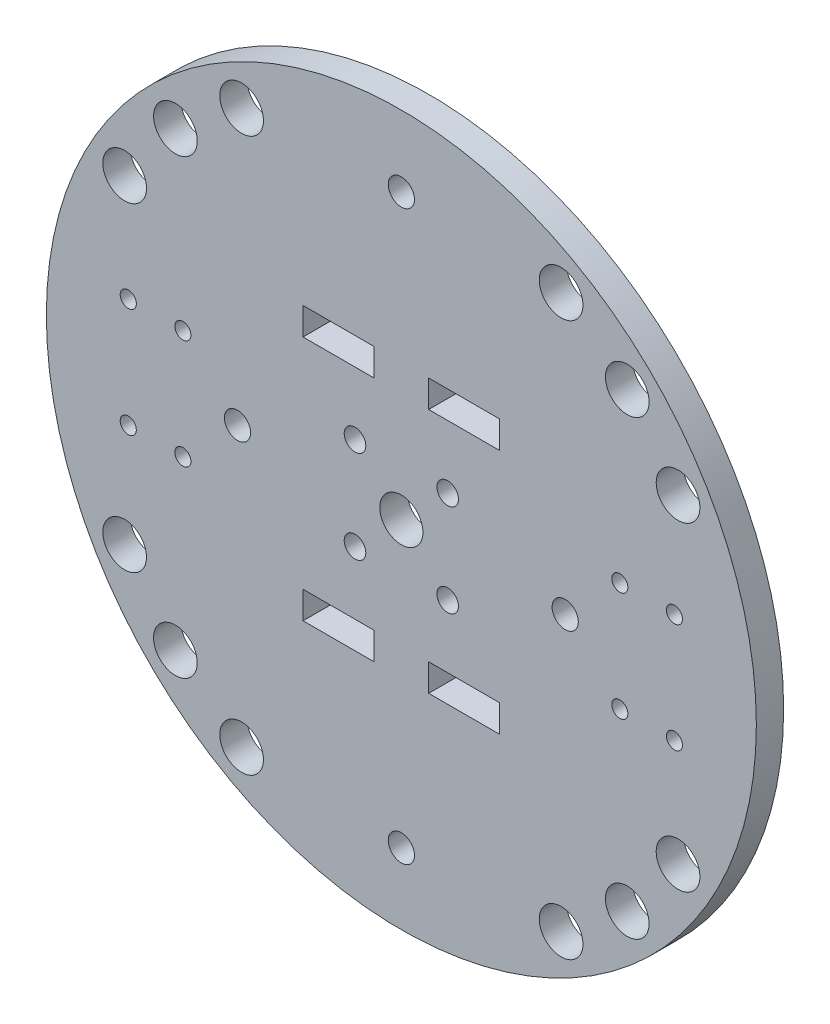
SolidWorks part; units mm, degrees
ref_plane "Front Plane" through (0, 0, 0) normal (0, 0, 1) x (1, 0, 0)
ref_plane "Top Plane" through (0, 0, 0) normal (0, 1, 0) x (1, 0, 0)
ref_plane "Right Plane" through (0, 0, 0) normal (1, 0, 0) x (0, 0, -1)
sketch "Sketch1" plane through (0, 0, 0) normal (0, 0, 1) x (1, 0, 0)
  line L0 (0, 0) -> (0, 65) construction
  line L1 (0, 0) -> (-65, 0) construction
  line L2 (18, 25) -> (18, 20)
  line L3 (-18, 25) -> (-5, 25)
  line L4 (-18, 25) -> (-18, 20)
  line L5 (-18, 20) -> (-5, 20)
  line L6 (-5, 25) -> (-5, 20)
  line L7 (18, 20) -> (5, 20)
  line L8 (5, 25) -> (5, 20)
  line L9 (18, 25) -> (5, 25)
  line L10 (5, -25) -> (5, -20)
  line L11 (18, -20) -> (5, -20)
  line L12 (18, -25) -> (18, -20)
  line L13 (18, -25) -> (5, -25)
  line L14 (-18, -25) -> (-18, -20)
  line L15 (-18, -25) -> (-5, -25)
  line L16 (-5, -25) -> (-5, -20)
  line L17 (-18, -20) -> (-5, -20)
  line L18 (0, 0) -> (-45.9619, 45.9619) construction
  line L19 (0, 0) -> (-32.5, 56.2917) construction
  line L20 (0, 0) -> (-56.2917, 32.5) construction
  circle A0 centre (0, 0) radius 65
  circle A1 centre (0, 0) radius 3.95
  circle A2 centre (0, 52) radius 2.4
  circle A3 centre (-30, 0) radius 2.4
  circle A4 centre (0, -52) radius 2.4
  circle A5 centre (30, 0) radius 2.4
  circle A6 centre (-41.3657, 41.3657) radius 4
  circle A7 centre (-29.25, 50.6625) radius 4
  circle A8 centre (-50.6625, 29.25) radius 4
  circle A9 centre (50.6625, 29.25) radius 4
  circle A10 centre (41.3657, 41.3657) radius 4
  circle A11 centre (29.25, 50.6625) radius 4
  circle A12 centre (50.6625, -29.25) radius 4
  circle A13 centre (41.3657, -41.3657) radius 4
  circle A14 centre (29.25, -50.6625) radius 4
  circle A15 centre (-29.25, -50.6625) radius 4
  circle A16 centre (-41.3657, -41.3657) radius 4
  circle A17 centre (-50.6625, -29.25) radius 4
  circle A18 centre (-40, 10) radius 1.475
  circle A19 centre (-50, 10) radius 1.475
  circle A20 centre (-40, -10) radius 1.475
  circle A21 centre (-50, -10) radius 1.475
  circle A22 centre (50, -10) radius 1.475
  circle A23 centre (40, -10) radius 1.475
  circle A24 centre (40, 10) radius 1.475
  circle A25 centre (50, 10) radius 1.475
  circle A26 centre (-8.4853, 8.4853) radius 1.975
  circle A27 centre (8.4853, 8.4853) radius 1.975
  circle A28 centre (8.4853, -8.4853) radius 1.975
  circle A29 centre (-8.4853, -8.4853) radius 1.975
  point P84 (0, 0)
  dimension "D1" = 130
  dimension "D2" = 7.9
  dimension "D3" = 4.8
  dimension "D5" = 4.8
  dimension "D12" = 8
  dimension "D16" = 8
  dimension "D18" = 8
  dimension "D20" = 2.95
  dimension "D23" = 2.95
  dimension "D26" = 3.95
  dimension "D4" = 52
  dimension "D6" = 30
  dimension "D7" = 5
  dimension "D8" = 13
  dimension "D9" = 5
  dimension "D10" = 20
  dimension "D11" = 45
  dimension "D13" = 58.5
  dimension "D14" = 15
  dimension "D15" = 15
  dimension "D17" = 58.5
  dimension "D19" = 58.5
  dimension "D21" = 40
  dimension "D22" = 10
  dimension "D24" = 10
  dimension "D25" = 10
  dimension "D27" = 12
  dimension "D28" = 4
extrude "Boss-Extrude1" add sketch "Sketch1" along normal blind 5
